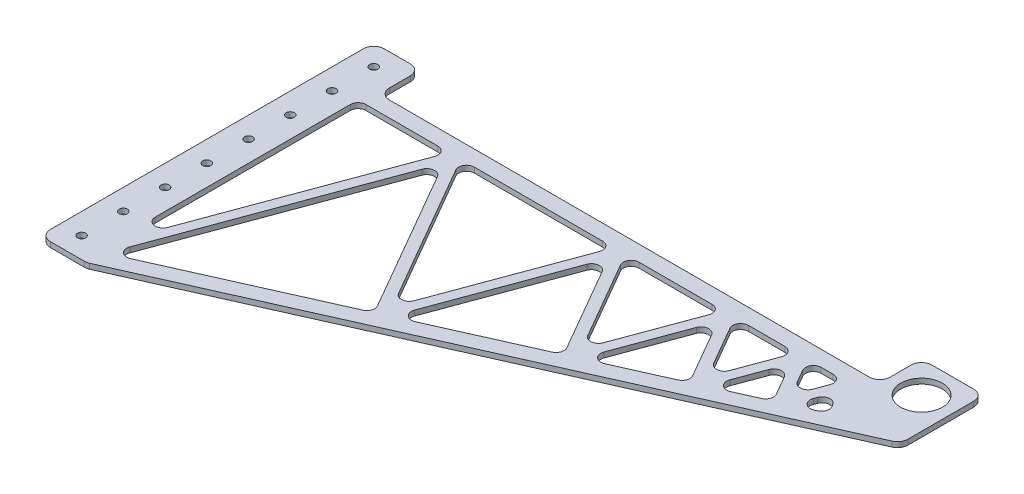
SolidWorks part; units mm, degrees
material "6061-T6 (SS)"
ref_plane "Front Plane" through (0, 0, 0) normal (0, 0, 1) x (1, 0, 0)
ref_plane "Top Plane" through (0, 0, 0) normal (0, 1, 0) x (1, 0, 0)
ref_plane "Right Plane" through (0, 0, 0) normal (1, 0, 0) x (0, 0, -1)
sketch "Sketch1" plane through (0, 0, 0) normal (0, 1, 0) x (1, 0, 0)
  line L0 (0, 0) -> (0, 203.2)
  line L1 (0, 203.2) -> (28.575, 203.2)
  line L2 (28.575, 203.2) -> (28.575, 177.8)
  line L3 (28.575, 177.8) -> (333.375, 177.8)
  line L4 (333.375, 177.8) -> (333.375, 203.2)
  line L5 (333.375, 203.2) -> (371.475, 203.2)
  line L6 (371.475, 203.2) -> (371.475, 152.6689)
  line L7 (371.475, 152.6689) -> (28.575, 0)
  line L8 (28.575, 0) -> (0, 0)
  dimension "D1" = 28.575
  dimension "D2" = 24
  dimension "D3" = 304.8
  dimension "D4" = 203.2
  dimension "D5" = 25.4
  dimension "D6" = 38.1
extrude "Boss-Extrude1" add sketch "Sketch1" along normal mid plane 3.175
sketch "Sketch2" plane through (0, 1.5875, 0) normal (0, 1, 0) x (1, 0, 0)
  line L0 (12.7, 203.2) -> (12.7, 0) construction
  line L1 (28.575, 203.2) -> (0, 203.2) construction
  line L2 (0, 0) -> (28.575, 0) construction
  line L3 (0, 203.2) -> (0, 0) construction
  line L4 (352.425, 203.2) -> (352.425, 142.9005) construction
  line L5 (371.475, 203.2) -> (333.375, 203.2) construction
  line L6 (333.375, 184.15) -> (371.475, 184.15) construction
  line L7 (333.375, 203.2) -> (333.375, 177.8) construction
  line L8 (371.475, 152.6689) -> (371.475, 203.2) construction
  line L9 (371.475, 203.2) -> (333.375, 203.2) construction
  circle A0 centre (12.7, 190.5) radius 2.4892
  circle A1 centre (12.7, 165.1) radius 2.4892
  circle A2 centre (12.7, 139.7) radius 2.4892
  circle A3 centre (12.7, 114.3) radius 2.4892
  circle A4 centre (12.7, 88.9) radius 2.4892
  circle A5 centre (12.7, 63.5) radius 2.4892
  circle A6 centre (12.7, 38.1) radius 2.4892
  circle A7 centre (12.7, 12.7) radius 2.4892
  circle A8 centre (352.425, 184.15) radius 12.7
  dimension "D1" = 4.9784
  dimension "D3" = 12.7
  dimension "D6" = 25.4
  dimension "D2" = 12.7
  dimension "D5" = 25.4
  dimension "D7" = 19.05
  dimension "D4" = 8
extrude "Cut-Extrude1" cut sketch "Sketch2" against normal through all
fillet "Fillet1" radius 6.35 9 edges at (0, 0, 0) (0, 0, -203.2) (28.575, 0, -177.8) (333.375, 0, -177.8) (333.375, 0, -203.2) (371.475, 0, -203.2) (371.475, 0, -152.6689) (28.575, 0, 0) (28.575, 0, -203.2)
sketch "Sketch3" plane through (0, 1.5875, 0) normal (0, 1, 0) x (1, 0, 0)
  line L0 (28.5209, 26.6247) -> (83.5957, 175.7225) construction
  line L1 (25.4, 9.0128) -> (84.2293, 168.275) construction
  line L2 (327.025, 177.8) -> (34.925, 177.8) construction
  line L3 (84.2293, 168.275) -> (145.3468, 62.4165) construction
  line L4 (145.3468, 62.4165) -> (184.4495, 168.275) construction
  line L5 (184.4495, 168.275) -> (225.073, 97.913) construction
  line L6 (29.808, 0.549) -> (367.7078, 150.9916) construction
  line L7 (225.073, 97.913) -> (251.0638, 168.275) construction
  line L8 (251.0638, 168.275) -> (278.0655, 121.5067) construction
  line L9 (278.0655, 121.5067) -> (295.3411, 168.275) construction
  line L10 (295.3411, 168.275) -> (313.2885, 137.189) construction
  line L11 (313.2885, 137.189) -> (324.7713, 168.275) construction
  line L12 (324.7713, 168.275) -> (336.7006, 147.6128) construction
  line L13 (34.4775, 24.4245) -> (84.863, 160.8275) construction
  line L14 (84.863, 160.8275) -> (145.9804, 54.969) construction
  line L15 (145.9804, 54.969) -> (185.0831, 160.8275) construction
  line L16 (83.5957, 175.7225) -> (144.7131, 69.8641) construction
  line L17 (144.7131, 69.8641) -> (183.8158, 175.7225) construction
  line L18 (185.0831, 160.8275) -> (225.7067, 90.4654) construction
  line L19 (225.7067, 90.4654) -> (251.6975, 160.8275) construction
  line L20 (251.6975, 160.8275) -> (278.6992, 114.0592) construction
  line L21 (278.6992, 114.0592) -> (295.9747, 160.8275) construction
  line L22 (295.9747, 160.8275) -> (313.9222, 129.7415) construction
  line L23 (29.4509, 10.8164) -> (87.614, 168.275)
  line L24 (80.7348, 167.9777) -> (142.4303, 61.118)
  line L25 (149.3977, 64.2201) -> (187.8342, 168.275)
  line L26 (180.955, 167.9777) -> (222.1565, 96.6145)
  line L27 (229.1239, 99.7165) -> (254.4485, 168.275)
  line L28 (247.5693, 167.9777) -> (275.149, 120.2082)
  line L29 (282.1164, 123.3103) -> (298.7258, 168.275)
  line L30 (291.8466, 167.9777) -> (310.3721, 135.8905)
  line L31 (317.3395, 138.9926) -> (328.156, 168.275)
  line L32 (25.4, 153.8624) -> (25.4, 26.3902)
  line L33 (25.4, 26.3902) -> (308.4227, 152.4)
  line L34 (308.4227, 152.4) -> (34.925, 152.4)
  line L35 (25.4, 168.275) -> (25.4, 9.0128)
  line L36 (25.4, 9.0128) -> (383.1087, 168.275)
  line L37 (383.1087, 168.275) -> (25.4, 168.275)
  line L38 (321.2768, 167.9777) -> (333.7841, 146.3143)
  line L39 (25.4, 18.1758) -> (80.8447, 168.275)
  line L40 (87.8955, 168.275) -> (148.2632, 63.715)
  line L41 (141.8522, 62.1192) -> (181.0648, 168.275)
  line L42 (188.1156, 168.275) -> (227.9895, 99.2115)
  line L43 (221.5785, 97.6156) -> (247.6791, 168.275)
  line L44 (254.73, 168.275) -> (280.982, 122.8052)
  line L45 (274.571, 121.2094) -> (291.9564, 168.275)
  line L46 (299.0072, 168.275) -> (316.205, 138.4876)
  line L47 (309.794, 136.8917) -> (321.3866, 168.275)
  line L48 (328.4375, 168.275) -> (339.6171, 148.9113)
  line L49 (313.9222, 129.7415) -> (325.405, 160.8275) construction
  line L50 (325.405, 160.8275) -> (333.951, 146.0253) construction
  line L51 (324.1376, 175.7225) -> (339.4503, 149.2003) construction
  line L52 (183.8158, 175.7225) -> (224.4393, 105.3605) construction
  line L53 (224.4393, 105.3605) -> (250.4302, 175.7225) construction
  line L54 (250.4302, 175.7225) -> (277.4318, 128.9543) construction
  line L55 (277.4318, 128.9543) -> (294.7074, 175.7225) construction
  line L56 (294.7074, 175.7225) -> (312.6549, 144.6366) construction
  line L57 (312.6549, 144.6366) -> (324.1376, 175.7225) construction
  line L58 (31.4992, 25.5246) -> (84.2293, 168.275) construction
  line L59 (371.475, 156.7927) -> (371.475, 196.85) construction
  arc A20 (25.4, 153.8624) -> (34.925, 152.4) centre (34.925, 184.15) ccw
  dimension "D1" = 50.8
  dimension "D3" = 9.525
  dimension "D4" = 9.525
  dimension "D7" = 30
  dimension "D2" = 25.4
  dimension "D5" = 3.175
  dimension "D6" = 3.175
extrude "Cut-Extrude2" cut sketch "Sketch3" against normal through all contours L24 L37 L23 L36 | L36 L39 L37 L35 | L36 L41 L37 L40 | L26 L37 L25 L36 | L36 L43 L37 L42 | L28 L37 L27 L36 | L36 L45 L37 L44 | L30 L37 L29 L36 | L36 L47 L37 L46 | L38 L37 L31 L36
fillet "Fillet2" radius 4.7625 30 edges at (275.149, 0, -120.2082) (229.1239, 0, -99.7165) (251.6975, 0, -160.8275) (310.3721, 0, -135.8905) (282.1164, 0, -123.3103) (295.9747, 0, -160.8275) (222.1565, 0, -96.6145) (149.3977, 0, -64.2201) (185.0831, 0, -160.8275) (317.3395, 0, -138.9926) (325.405, 0, -160.8275) (333.7841, 0, -146.3143) (142.4303, 0, -61.118) (29.4509, 0, -10.8164) (84.863, 0, -160.8275) (188.1156, 0, -168.275) (247.6791, 0, -168.275) (224.4393, 0, -105.3605) (87.8955, 0, -168.275) (181.0648, 0, -168.275) (144.7131, 0, -69.8641) (25.4, 0, -168.275) (80.8447, 0, -168.275) (25.4, 0, -18.1758) (321.3866, 0, -168.275) (312.6549, 0, -144.6366) (254.73, 0, -168.275) (291.9564, 0, -168.275) (277.4318, 0, -128.9543) (299.0072, 0, -168.275)
